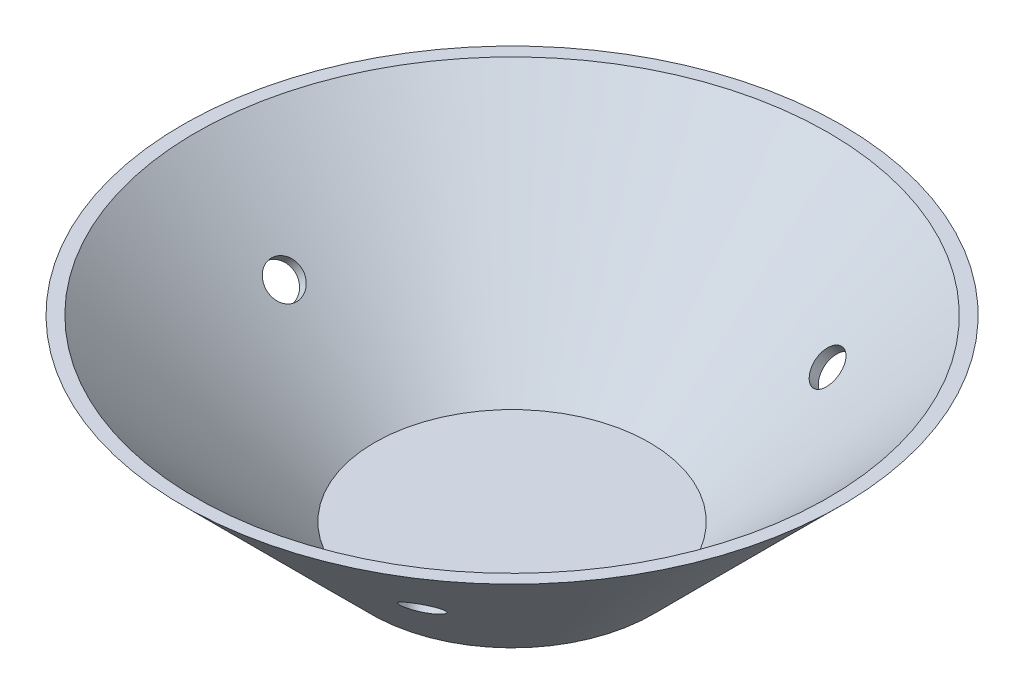
SolidWorks part; units mm, degrees
ref_plane "Alzado" through (0, 0, 0) normal (0, 0, 1) x (1, 0, 0)
ref_plane "Planta" through (0, 0, 0) normal (0, 1, 0) x (1, 0, 0)
ref_plane "Vista lateral" through (0, 0, 0) normal (1, 0, 0) x (0, 0, -1)
sketch "Croquis1" [suppressed] plane through (0, 0, 0) normal (0, 0, 1) x (1, 0, 0)
  circle A0 centre (0, 0) radius 35
  circle A1 centre (0, 0) radius 12.5 construction
  dimension "D1" = 70
  dimension "D2" = 25
sketch "Croquis4" plane through (0, 0, 0) normal (1, 0, 0) x (0, 0, -1)
  line L0 (0, 0) -> (-15, 0)
  line L1 (-15, 0) -> (-35, 20)
  line L2 (-35, 20) -> (0, 20)
  line L3 (0, 20) -> (0, 0)
  line L4 (0, 0) -> (0, 67.2663) construction
  line L5 (0, 1) -> (-14.5858, 1)
  line L6 (-14.5858, 1) -> (-33.5858, 20)
  line L7 (-14.5858, 1) -> (-34.2929, 20.7071) construction
  line L8 (-33.5858, 20) -> (-35, 20)
  line L9 (0, 1) -> (0, 0)
  dimension "D1" = 45
  dimension "D2" = 35
  dimension "D3" = 20
  dimension "D4" = 1
revolve "Revolución1" add sketch "Croquis4" angle 360 about L4
ref_plane "Plano1" through (-7.5, -7.5, 0) normal (-0.7071, -0.7071, 0) x (0, 0, 1)
sketch "Croquis5" plane through (-7.5, -7.5, -10.6066) normal (0.7071, 0.7071, 0) x (0.5, -0.5, -0.7071)
  circle A1 centre (-25, 10.3536) radius 1.9
  ellipse E0 centre (-8, -7) end of major axis (2.3137, 3.3137) minor radius 10.3137 construction
  dimension "D1" = 3.8
  dimension "D2" = 17
  dimension "D3" = 25
extrude "Cortar-Extruir1" cut sketch "Croquis5" along normal through all
pattern_circular "MatrizC1" count 3 over 360 about axis through (0, 1, 0) along (0, 1, 0) of "Cortar-Extruir1"
